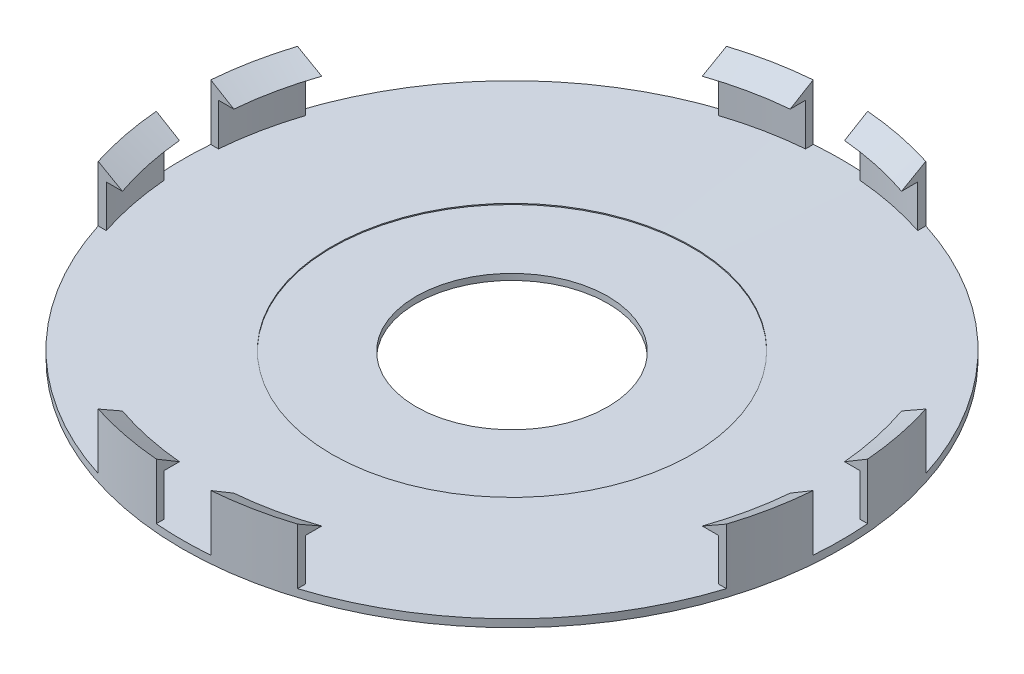
SolidWorks part; units mm, degrees
ref_plane "Спереди" through (0, 0, 0) normal (0, 0, 1) x (1, 0, 0)
ref_plane "Сверху" through (0, 0, 0) normal (0, 1, 0) x (1, 0, 0)
ref_plane "Справа" through (0, 0, 0) normal (1, 0, 0) x (0, 0, -1)
other "Configuration Table"
sketch "Эскиз2" plane through (0, 0, 0) normal (0, 0, 1) x (1, 0, 0)
  line L0 (0, -20.6024) -> (0, 34.9584) construction
  line L1 (12.5, 0) -> (12.5, 0.8969)
  line L2 (12.5, 0.8969) -> (42, 1)
  line L3 (42, 1) -> (42, 6.5)
  line L4 (42, 6.5) -> (40, 6.5)
  line L7 (43, 8.3) -> (43, 0)
  line L8 (43, 0) -> (12.5, 0)
  line L9 (40, 6.5) -> (43, 8.3)
  point P7 (0, 0)
  point P9 (0, 0)
  point P12 (0, 0)
  point P13 (0, 0)
  point P14 (0, 0)
revolve "Повернуть1" add sketch "Эскиз2" angle 360 about L0
ref_plane "Плоскость1" through (0, 8.3, 0) normal (0, 1, 0) x (1, 0, 0)
sketch "Эскиз3" plane through (0, 8.3, 0) normal (0, 1, 0) x (1, 0, 0)
  line L0 (-13, 43.0329) -> (-13, -46.439) construction
  line L1 (-43.7391, -13) -> (45.6498, -13) construction
  line L2 (-13, -13) -> (-53, -13)
  line L3 (-53, -13) -> (-13, -53)
  line L4 (-13, -53) -> (-13, -13)
  line L5 (-13, 13) -> (-13, 53)
  line L6 (-13, 53) -> (-53, 13)
  line L7 (-53, 13) -> (-13, 13)
  line L8 (13, 13) -> (53, 13)
  line L9 (53, 13) -> (13, 53)
  line L10 (13, 53) -> (13, 13)
  line L11 (13, -13) -> (13, -53)
  line L12 (13, -53) -> (53, -13)
  line L13 (53, -13) -> (13, -13)
  line L14 (-3.55, 53) -> (-3.55, 28.7336)
  line L15 (-53, 3.55) -> (-28.7336, 3.55)
  line L16 (-53, 3.55) -> (-53, -3.55)
  line L17 (-53, -3.55) -> (-28.7336, -3.55)
  line L18 (-28.7336, 3.55) -> (-28.7336, -3.55)
  line L19 (3.55, 53) -> (-3.55, 53)
  line L20 (3.55, 53) -> (3.55, 28.7336)
  line L21 (3.55, 28.7336) -> (-3.55, 28.7336)
  line L22 (53, 3.55) -> (28.7336, 3.55)
  line L23 (53, -3.55) -> (53, 3.55)
  line L24 (53, -3.55) -> (28.7336, -3.55)
  line L25 (28.7336, -3.55) -> (28.7336, 3.55)
  line L26 (3.55, -53) -> (3.55, -28.7336)
  line L27 (-3.55, -53) -> (3.55, -53)
  line L28 (-3.55, -53) -> (-3.55, -28.7336)
  line L29 (-3.55, -28.7336) -> (3.55, -28.7336)
  point P19 (0, 0)
  dimension "D1" = 4
extrude "Вырез-Вытянуть1" cut sketch "Эскиз3" against normal up to surface (7.256 mm away)
sketch "Эскиз4" plane through (0, 8.3, 0) normal (0, 1, 0) x (1, 0, 0)
  circle A0 centre (0, 0) radius 23.5
extrude "Вырез-Вытянуть2" cut sketch "Эскиз4" against normal blind 7.5
